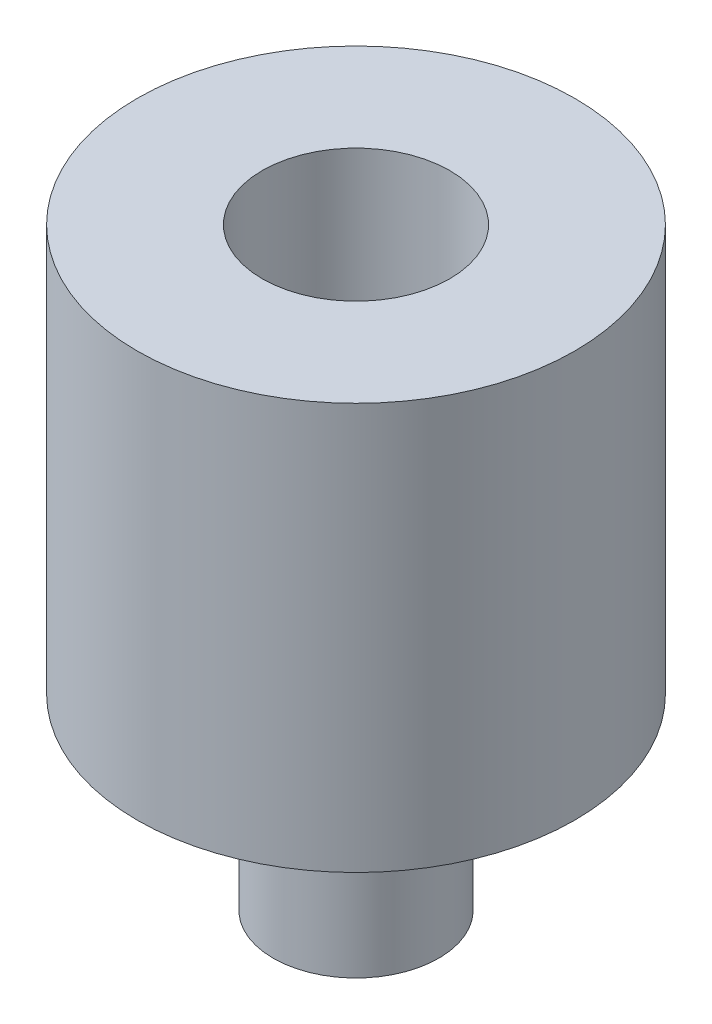
SolidWorks part; units mm, degrees
ref_plane "Front Plane" through (0, 0, 0) normal (0, 0, 1) x (1, 0, 0)
ref_plane "Top Plane" through (0, 0, 0) normal (0, 1, 0) x (1, 0, 0)
ref_plane "Right Plane" through (0, 0, 0) normal (1, 0, 0) x (0, 0, -1)
sketch "Sketch1" plane through (0, 0, 0) normal (0, 1, 0) x (1, 0, 0)
  circle A0 centre (0, 0) radius 1.325
  dimension "D1" = 2.65
extrude "Boss-Extrude1" add sketch "Sketch1" along normal blind 3
sketch "Sketch2" plane through (0, 3, 0) normal (0, 1, 0) x (1, 0, 0)
  circle A0 centre (0, 0) radius 3.5
extrude "Boss-Extrude2" add sketch "Sketch2" along normal blind 1.5
sketch "Sketch3" plane through (0, 4.5, 0) normal (0, 1, 0) x (1, 0, 0)
  circle A0 centre (0, 0) radius 1.5
  circle A1 centre (0, 0) radius 3.5
extrude "Boss-Extrude3" add sketch "Sketch3" along normal blind 5
